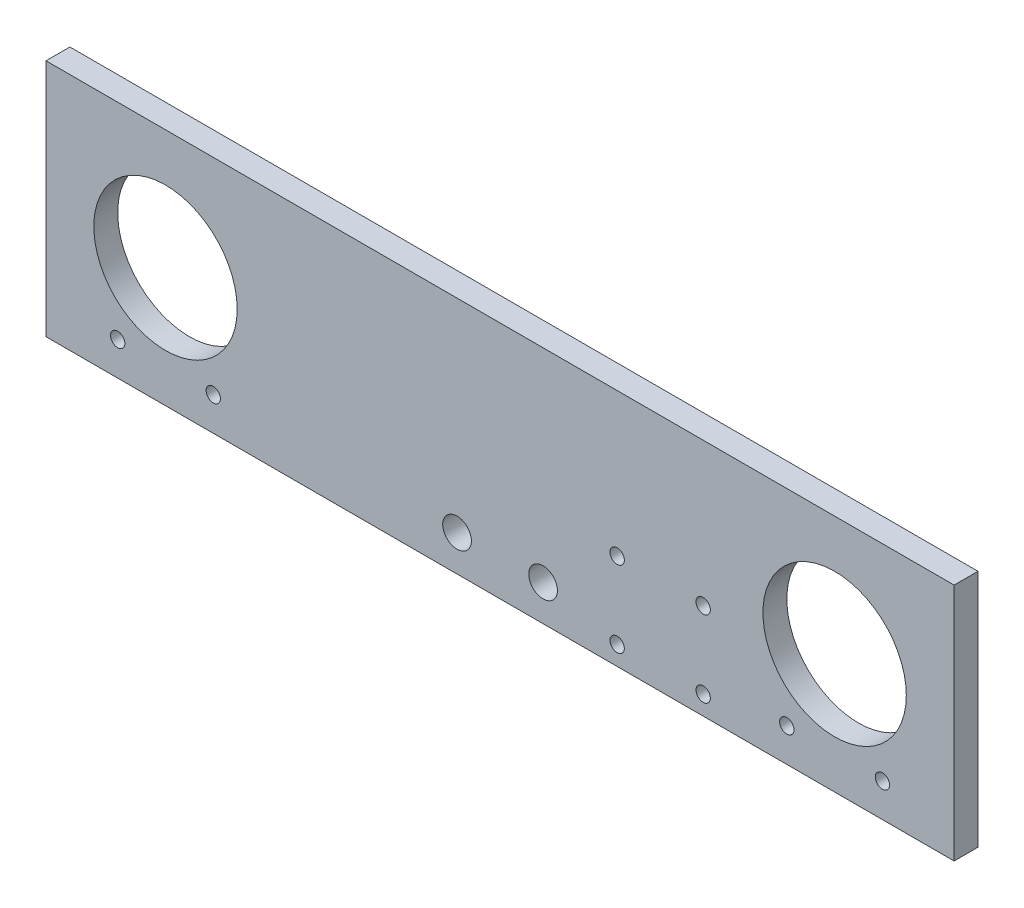
SolidWorks part; units mm, degrees
ref_plane "Front Plane" through (0, 0, 0) normal (0, 0, 1) x (1, 0, 0)
ref_plane "Top Plane" through (0, 0, 0) normal (0, 1, 0) x (1, 0, 0)
ref_plane "Right Plane" through (0, 0, 0) normal (1, 0, 0) x (0, 0, -1)
sketch "Sketch1" plane through (0, 0, 0) normal (0, 0, 1) x (1, 0, 0)
  line L1 (0, 0) -> (190, 0)
  line L2 (0, 0) -> (0, 50)
  line L3 (0, 50) -> (190, 50)
  line L4 (190, 0) -> (190, 50)
  circle A0 centre (25, 25) radius 15
  circle A1 centre (165, 25) radius 15
  circle A2 centre (35, 7) radius 1.5
  circle A3 centre (175, 7) radius 1.5
  circle A4 centre (155, 7) radius 1.5
  circle A5 centre (137.5, 4) radius 1.5
  circle A6 centre (86, 7.5) radius 3
  circle A7 centre (104, 7.5) radius 3
  circle A8 centre (15, 7) radius 1.5
  circle A9 centre (119.5, 4) radius 1.5
  circle A10 centre (119.5, 20) radius 1.5
  circle A11 centre (137.5, 20) radius 1.5
  point P5 (95, 25)
  dimension "D3" = 30
  dimension "D7" = 30
  dimension "D9" = 3
  dimension "D11" = 7
  dimension "D15" = 3
  dimension "D16" = 7
  dimension "D23" = 95
  dimension "D24" = 6
  dimension "D28" = 27.5
  dimension "D29" = 3
  dimension "D25" = 6
  dimension "D14" = 10
  dimension "D12" = 3
  dimension "D19" = 18
  dimension "D2" = 50
  dimension "D4" = 70
  dimension "D5" = 70
  dimension "D6" = 25
  dimension "D8" = 95
  dimension "D10" = 10
  dimension "D13" = 7
  dimension "D17" = 10
  dimension "D18" = 10
  dimension "D20" = 7
  dimension "D21" = 25
  dimension "D22" = 25
  dimension "D26" = 7.5
  dimension "D27" = 7.5
  dimension "D30" = 4
  dimension "D31" = 16
  dimension "D32" = 9
  dimension "D35" = 9
extrude "Boss-Extrude1" add sketch "Sketch1" along normal blind 5
sketch "Sketch2" plane through (0, 0, 5) normal (0, 0, 1) x (1, 0, 0)
  circle A0 centre (15, 7) radius 2.75
  circle A1 centre (35, 7) radius 2.75
  circle A2 centre (155, 7) radius 2.75
  circle A3 centre (175, 7) radius 2.75
  dimension "D1" = 5.5
extrude "Cut-Extrude1" cut sketch "Sketch2" along normal blind 1.5 from surface
